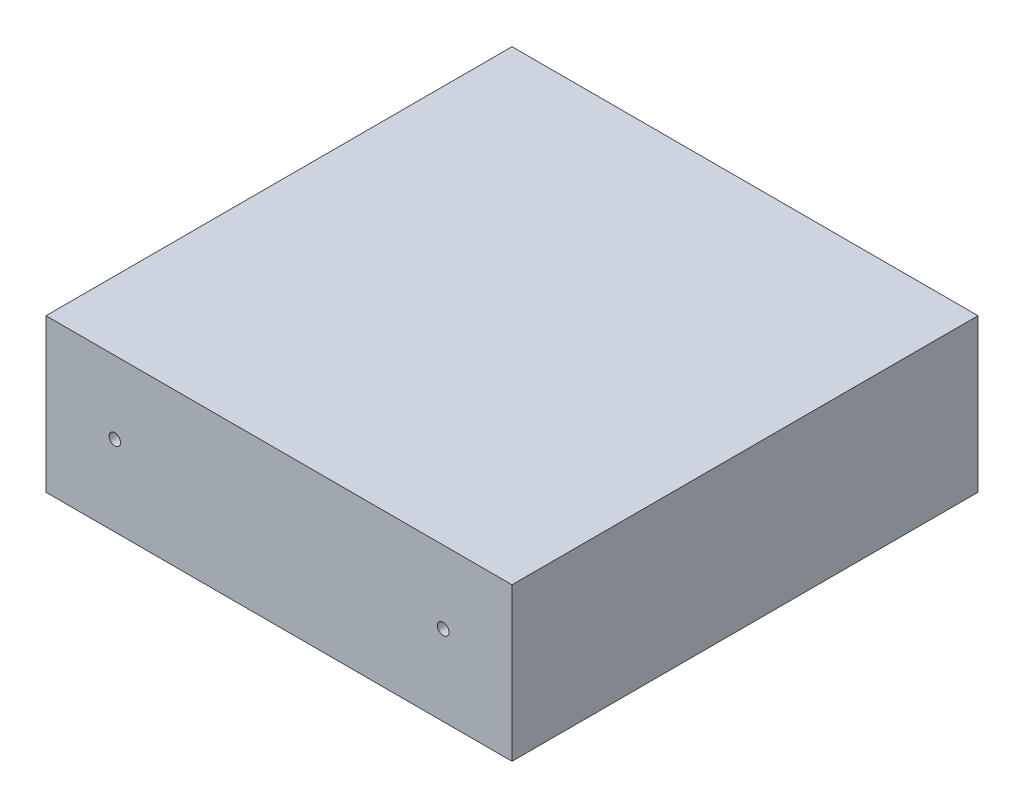
SolidWorks part; units mm, degrees
material "PVC Rigid"
ref_plane "Front Plane" through (0, 0, 0) normal (0, 0, 1) x (1, 0, 0)
ref_plane "Top Plane" through (0, 0, 0) normal (0, 1, 0) x (1, 0, 0)
ref_plane "Right Plane" through (0, 0, 0) normal (1, 0, 0) x (0, 0, -1)
sketch "Sketch1" plane through (0, 0, 0) normal (0, 1, 0) x (1, 0, 0)
  line L1 (0, 0) -> (406.4, 0)
  line L2 (0, 0) -> (0, 406.4)
  line L3 (0, 406.4) -> (406.4, 406.4)
  line L4 (406.4, 0) -> (406.4, 406.4)
  dimension "D1" = 406.4
  dimension "D2" = 406.4
extrude "Boss-Extrude1" add sketch "Sketch1" along normal blind 133.35
sketch "Sketch2" plane through (0, 0, 0) normal (0, 0, 1) x (1, 0, 0)
  line L0 (406.4, 133.35) -> (406.4, 0) construction
  circle A0 centre (60, 70) radius 5
  circle A1 centre (346.4, 70) radius 5
  dimension "D1" = 10
  dimension "D2" = 10
  dimension "D3" = 60
  dimension "D4" = 70
  dimension "D6" = 0
  dimension "D7" = 60
extrude "Cut-Extrude1" cut sketch "Sketch2" against normal through all
